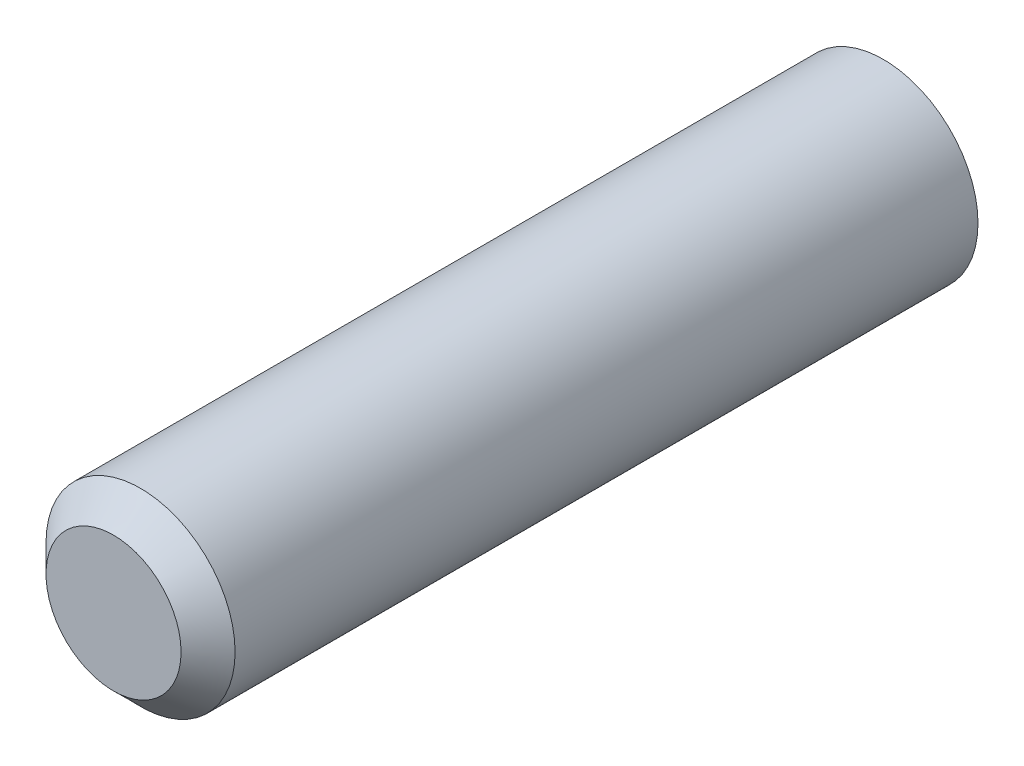
SolidWorks part; units mm, degrees
ref_plane "Plano frontal" through (0, 0, 0) normal (0, 0, 1) x (1, 0, 0)
ref_plane "Plano superior" through (0, 0, 0) normal (0, 1, 0) x (1, 0, 0)
ref_plane "Plano direito" through (0, 0, 0) normal (1, 0, 0) x (0, 0, -1)
sketch "Esboço1" plane through (0, 0, 0) normal (0, 0, 1) x (1, 0, 0)
  circle A0 centre (0, 0) radius 70
extrude "Ressalto-extrusão1" add sketch "Esboço1" along normal blind 570
chamfer "Chanfro1" distance 20 angle 45 1 edges at (70, 0, 570)
sketch "Esboço2" plane through (0, 0, 570) normal (0, 0, 1) x (1, 0, 0)
  circle A0 centre (0, 0) radius 70
curve "Hélice/Espiral1" pitch 35 height 542.5 turns 15.5
sketch "Esboço3" plane through (0, 0, 0) normal (1, 0, 0) x (0, 0, -1)
  line L0 (-579.6308, 59.136) -> (-570.9188, 74.2257)
  line L1 (-570.9188, 74.2257) -> (-592.7596, 74.2257)
  line L2 (-592.7596, 74.2257) -> (-584.0476, 59.136)
  line L3 (-550, 70) -> (-571.337, 70) construction
  circle A0 centre (-581.8392, 60.411) radius 2.55
  dimension "D3" = 5.1
  dimension "D1" = 60
  dimension "D2" = 60
